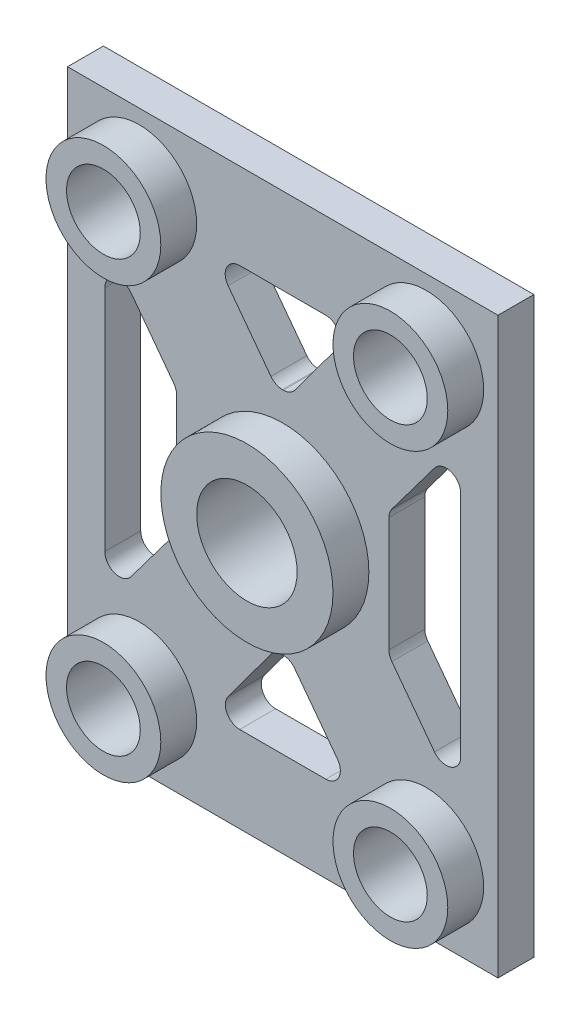
SolidWorks part; units mm, degrees
ref_plane "Front Plane" through (0, 0, 0) normal (0, 0, 1) x (1, 0, 0)
ref_plane "Top Plane" through (0, 0, 0) normal (0, 1, 0) x (1, 0, 0)
ref_plane "Right Plane" through (0, 0, 0) normal (1, 0, 0) x (0, 0, -1)
sketch "Sketch1" plane through (0, 0, 0) normal (0, 0, 1) x (1, 0, 0)
  line L1 (0, 0) -> (38.1, 0)
  line L2 (0, 0) -> (0, -50.8)
  line L3 (0, -50.8) -> (38.1, -50.8)
  line L4 (38.1, 0) -> (38.1, -50.8)
  circle A0 centre (6.35, -6.35) radius 3.2639
  circle A1 centre (6.35, -44.45) radius 3.2639
  circle A2 centre (31.75, -44.45) radius 3.2639
  circle A3 centre (31.75, -6.35) radius 3.2639
  circle A4 centre (19.05, -25.4) radius 4.445
  point P12 (19.05, 0)
  point P13 (0, -25.4)
  point P14 (0, 0)
  point P15 (0, 0)
  dimension "D3" = 6.5278
  dimension "D5" = 6.35
  dimension "D8" = 8.89
  dimension "D1" = 38.1
  dimension "D2" = 50.8
  dimension "D4" = 6.35
  dimension "D6" = 6.35
  dimension "D7" = 6.35
extrude "Base Extrude" add sketch "Sketch1" along normal blind 3.175
sketch "Sketch2" plane through (0, 0, 3.175) normal (0, 0, 1) x (1, 0, 0)
  circle A0 centre (19.05, -25.4) radius 4.445
  circle A1 centre (19.05, -25.4) radius 7.62
  circle A2 centre (19.05, -25.4) radius 4.445 construction
  circle A3 centre (6.35, -6.35) radius 5.08
  circle A4 centre (31.75, -6.35) radius 5.08
  circle A5 centre (6.35, -44.45) radius 5.08
  circle A6 centre (31.75, -44.45) radius 5.08
  circle A7 centre (6.35, -6.35) radius 3.2639
  circle A8 centre (31.75, -6.35) radius 3.2639
  circle A9 centre (6.35, -44.45) radius 3.2639
  circle A10 centre (31.75, -44.45) radius 3.2639
  dimension "D1" = 15.24
  dimension "D2" = 10.16
  dimension "D3" = 6.5278
extrude "Raiser" add sketch "Sketch2" along normal blind 3.175
sketch "Sketch3" plane through (0, 0, 3.175) normal (0, 0, 1) x (1, 0, 0)
  line L0 (3.302, -15.2897) -> (3.302, -35.5103)
  line L1 (5.6178, -36.2823) -> (9.3947, -31.2464)
  line L2 (9.652, -30.4745) -> (9.652, -20.3255)
  line L3 (9.3947, -19.5536) -> (5.6178, -14.5177)
  line L4 (15.24, -7.62) -> (22.86, -7.62)
  line L5 (23.8813, -9.6448) -> (20.1268, -14.7248)
  line L7 (18.0009, -14.732) -> (14.2108, -9.6785)
  line L8 (19.05, -25.4) -> (0, 0) construction
  line L9 (38.1, 0) -> (0, 0) construction
  line L10 (0, -50.8) -> (38.1, -50.8) construction
  line L11 (0, 0) -> (0, -50.8) construction
  line L12 (19.0169, -15.24) -> (19.1055, -15.24)
  line L13 (38.1, -50.8) -> (38.1, 0) construction
  line L14 (14.2187, -41.1552) -> (17.9732, -36.0752)
  line L15 (19.0831, -35.56) -> (18.9945, -35.56)
  line L16 (20.0991, -36.068) -> (23.8892, -41.1215)
  line L17 (22.86, -43.18) -> (15.24, -43.18)
  line L18 (28.7053, -31.2464) -> (32.4822, -36.2823)
  line L19 (34.798, -35.5103) -> (34.798, -15.2897)
  line L20 (32.4822, -14.5177) -> (28.7053, -19.5536)
  line L21 (28.448, -20.3255) -> (28.448, -30.4745)
  circle A0 centre (19.05, -25.4) radius 7.62 construction
  arc A1 (22.86, -7.62) -> (23.8813, -9.6448) centre (22.86, -8.89) cw
  arc A4 (15.24, -7.62) -> (14.2108, -9.6785) centre (15.24, -8.9066) ccw
  arc A5 (9.652, -20.3255) -> (9.3947, -19.5536) centre (8.3654, -20.3255) ccw
  arc A6 (9.3947, -31.2464) -> (9.652, -30.4745) centre (8.3654, -30.4745) ccw
  arc A7 (3.302, -35.5103) -> (5.6178, -36.2823) centre (4.5886, -35.5103) ccw
  arc A8 (3.302, -15.2897) -> (5.6178, -14.5177) centre (4.5886, -15.2897) cw
  arc A9 (19.1055, -15.24) -> (20.1268, -14.7248) centre (19.1055, -13.97) ccw
  arc A10 (19.0169, -15.24) -> (18.0009, -14.732) centre (19.0169, -13.97) cw
  arc A11 (18.9945, -35.56) -> (17.9732, -36.0752) centre (18.9945, -36.83) ccw
  arc A12 (19.0831, -35.56) -> (20.0991, -36.068) centre (19.0831, -36.83) cw
  arc A13 (22.86, -43.18) -> (23.8892, -41.1215) centre (22.86, -41.8934) ccw
  arc A14 (15.24, -43.18) -> (14.2187, -41.1552) centre (15.24, -41.91) cw
  arc A15 (34.798, -35.5103) -> (32.4822, -36.2823) centre (33.5114, -35.5103) cw
  arc A16 (28.448, -30.4745) -> (28.7053, -31.2464) centre (29.7346, -30.4745) ccw
  arc A17 (34.798, -15.2897) -> (32.4822, -14.5177) centre (33.5114, -15.2897) ccw
  arc A18 (28.7053, -19.5536) -> (28.448, -20.3255) centre (29.7346, -20.3255) ccw
  point P24 (25.3779, -7.62)
  point P28 (19.746, -15.24)
  point P31 (12.6669, -7.62)
  point P38 (3.302, -39.37)
  point P41 (3.302, -11.43)
  point P46 (18.3819, -15.24)
  point P71 (19.05, -25.4)
  dimension "D4" = 9.398
  dimension "D9" = 1.27
  dimension "D10" = 1.27
  dimension "D1" = 11.43
  dimension "D2" = 11.43
  dimension "D3" = 3.302
  dimension "D5" = 15.24
  dimension "D6" = 15.24
  dimension "D7" = 7.62
  dimension "D8" = 10.16
  dimension "D11" = 2
extrude "Weight Reduction - screw access" cut sketch "Sketch3" against normal through all
